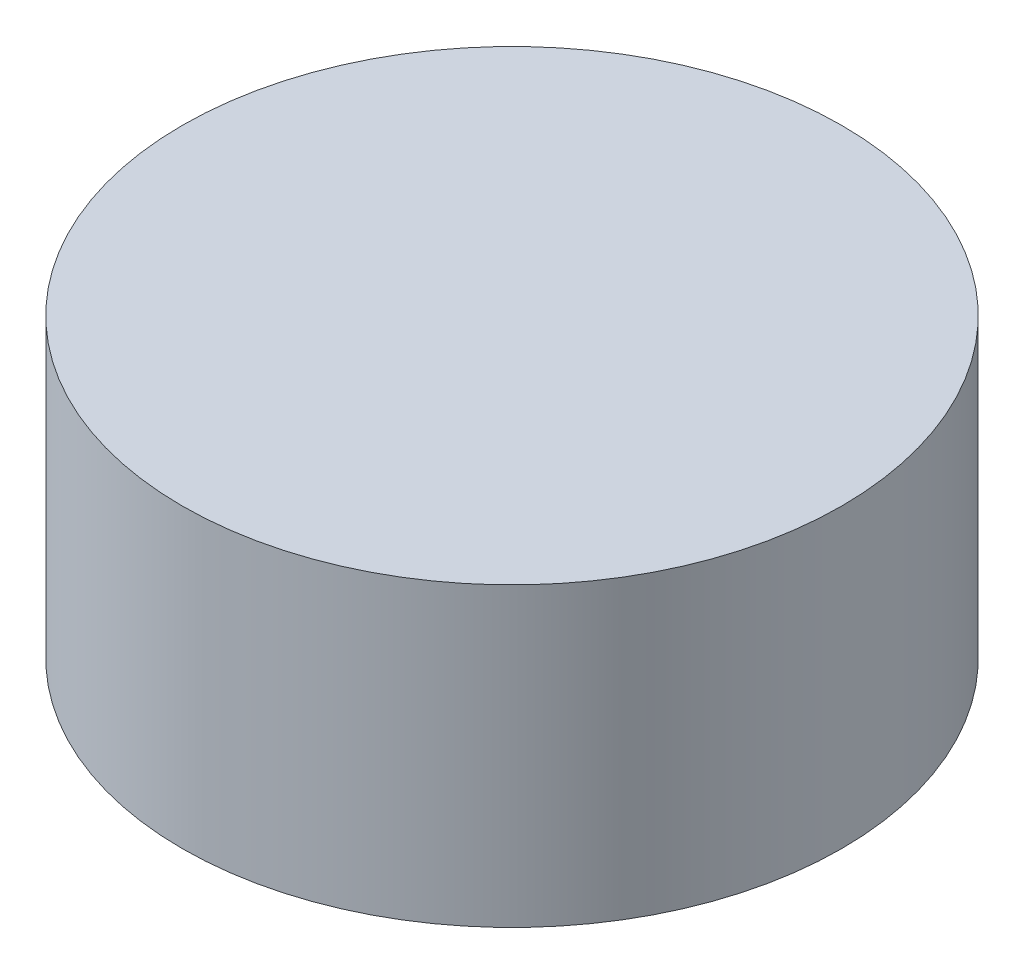
SolidWorks part; units mm, degrees
material "ﾒﾗﾐﾝ樹脂"
ref_plane "正面" through (0, 0, 0) normal (0, 0, 1) x (1, 0, 0)
ref_plane "平面" through (0, 0, 0) normal (0, 1, 0) x (1, 0, 0)
ref_plane "右側面" through (0, 0, 0) normal (1, 0, 0) x (0, 0, -1)
sketch "ｽｹｯﾁ1" plane through (0, 0, 0) normal (0, 1, 0) x (1, 0, 0)
  circle A0 centre (0, 0) radius 5
extrude "ﾎﾞｽ - 押し出し1" add sketch "ｽｹｯﾁ1" along normal blind 4.5
